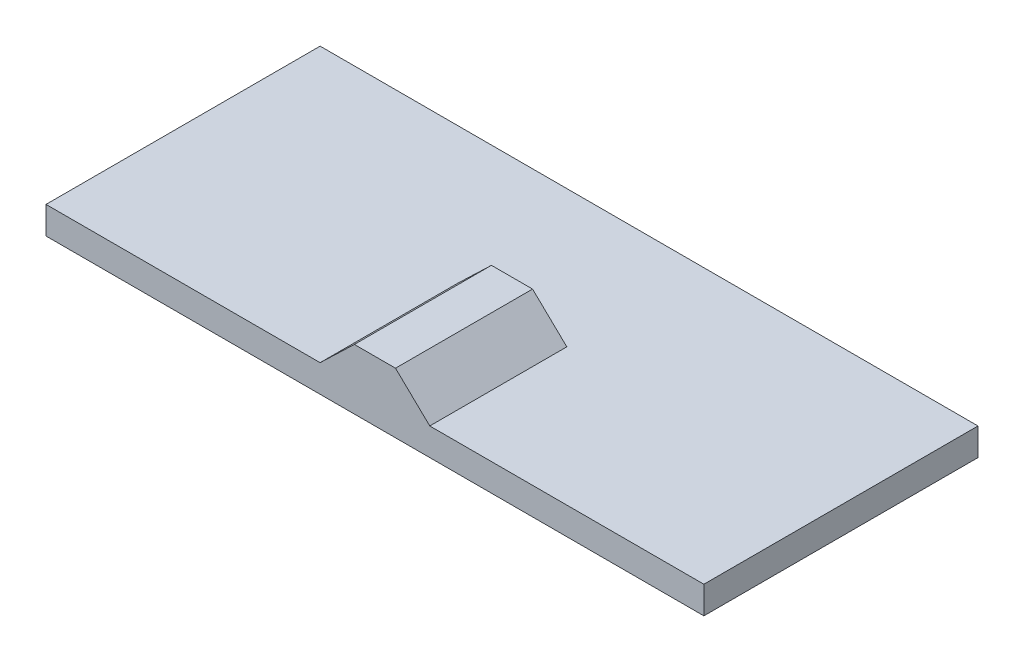
SolidWorks part; units mm, degrees
ref_plane "Front Plane" through (0, 0, 0) normal (0, 0, 1) x (1, 0, 0)
ref_plane "Top Plane" through (0, 0, 0) normal (0, 1, 0) x (1, 0, 0)
ref_plane "Right Plane" through (0, 0, 0) normal (1, 0, 0) x (0, 0, -1)
sketch "Sketch1" plane through (0, 0, 0) normal (0, 1, 0) x (1, 0, 0)
  line L1 (1800, -750) -> (-1800, -750)
  line L2 (1800, -750) -> (1800, 750)
  line L3 (1800, 750) -> (-1800, 750)
  line L4 (-1800, -750) -> (-1800, 750)
  line L5 (1800, -750) -> (-1800, 750) construction
  line L6 (1800, 750) -> (-1800, -750) construction
  point P0 (0, 0)
  dimension "D1" = 1500
  dimension "D2" = 3600
extrude "Boss-Extrude1" add sketch "Sketch1" along normal blind 150
sketch "Sketch3" plane through (0, 0, 750) normal (0, 0, 1) x (1, 0, 0)
  line L0 (0, 0) -> (0, 150) construction
  line L1 (-1800, 150) -> (1800, 150) construction
  line L2 (300, 150) -> (-300, 150)
  line L3 (-112.5, 330) -> (112.5, 330)
  line L4 (-300, 150) -> (-112.5, 330)
  line L5 (112.5, 330) -> (300, 150)
  point P5 (0, 330)
  point P8 (0, 150)
  dimension "D1" = 300
  dimension "D2" = 225
  dimension "D3" = 180
extrude "Boss-Extrude2" add sketch "Sketch3" along direction (0, 0, 1) on the side against the normal blind 750
